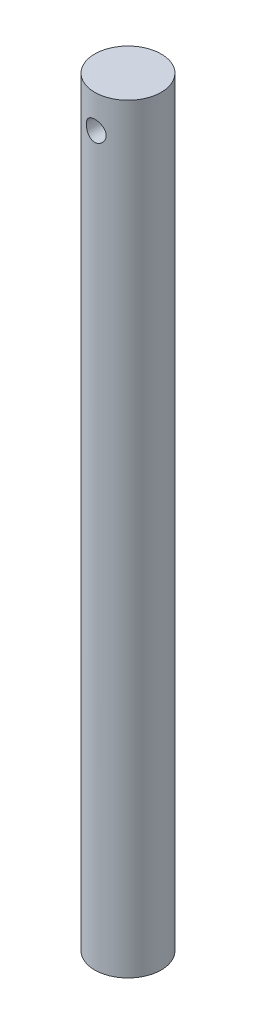
SolidWorks part; units mm, degrees
ref_plane "Front" through (0, 0, 0) normal (0, 0, 1) x (1, 0, 0)
ref_plane "Top" through (0, 0, 0) normal (0, 1, 0) x (1, 0, 0)
ref_plane "Right" through (0, 0, 0) normal (1, 0, 0) x (0, 0, -1)
sketch "Sketch1" plane through (0, 0, 0) normal (0, 1, 0) x (1, 0, 0)
  circle A0 centre (0, 0) radius 9.9949
  dimension "D1" = 19.9898
extrude "Boss-Extrude1" add sketch "Sketch1" along normal blind 228.6
sketch "Sketch2" plane through (0, 0, 0) normal (0, 0, 1) x (1, 0, 0)
  line L0 (9.9949, 228.6) -> (-9.9949, 228.6) construction
  circle A0 centre (0, 218.5924) radius 2.9972
  point P4 (0, 142.3924)
  dimension "D1" = 10.0076
  dimension "D2" = 5.9944
extrude "Cut-Extrude1" cut sketch "Sketch2" against normal through all both and the other way through all contours A0
